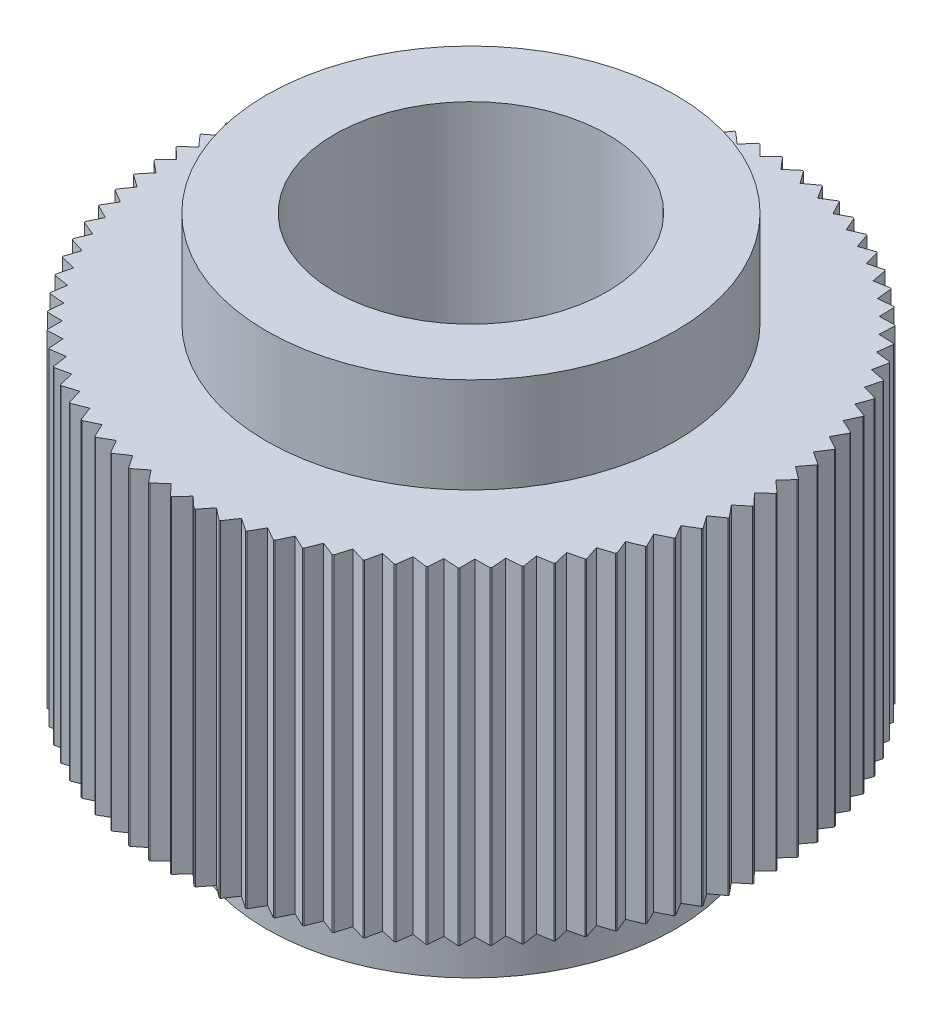
SolidWorks part; units mm, degrees
ref_plane "前视基准面" through (0, 0, 0) normal (0, 0, 1) x (1, 0, 0)
ref_plane "上视基准面" through (0, 0, 0) normal (0, 1, 0) x (1, 0, 0)
ref_plane "右视基准面" through (0, 0, 0) normal (1, 0, 0) x (0, 0, -1)
sketch "草图1" plane through (0, 0, 0) normal (0, 1, 0) x (1, 0, 0)
  circle A0 centre (0, 0) radius 11
  dimension "D1" = 22
extrude "凸台-拉伸1" add sketch "草图1" along normal blind 12
sketch "草图2" plane through (0, 0, 0) normal (0, -1, 0) x (1, 0, 0)
  circle A0 centre (0, 0) radius 7.5
  dimension "D1" = 15
extrude "凸台-拉伸2" add sketch "草图2" along normal blind 3.5
sketch "草图3" plane through (0, 12, 0) normal (0, 1, 0) x (1, 0, 0)
  circle A0 centre (0, 0) radius 7.5
  dimension "D1" = 15
extrude "凸台-拉伸3" add sketch "草图3" along normal blind 3.5
sketch "草图4" plane through (0, 15.5, 0) normal (0, 1, 0) x (1, 0, 0)
  circle A0 centre (0, 0) radius 5
  dimension "D1" = 10
extrude "切除-拉伸1" cut sketch "草图4" against normal through all
sketch "草图5" plane through (0, 12, 0) normal (0, 1, 0) x (1, 0, 0)
  line L0 (0, 0) -> (0, 11) construction
  line L1 (0, 10.6) -> (-0.393, 10.993)
  line L2 (0, 10.6) -> (0.393, 10.993)
  circle A0 centre (0, 0) radius 10.6 construction
  circle A1 centre (0, 0) radius 11
  circle A2 centre (0, 0) radius 11
  circle M2 centre (0, 0) radius 11
  dimension "D3" = 90
  dimension "D1" = 0
  dimension "D2" = 0.4
extrude "切除-拉伸2" cut sketch "草图5" against normal through all contours L1 L2 M2
pattern_circular "阵列(圆周)1" count 83 over 360 about axis through (0, 0, 0) along (0, 1, 0) of "切除-拉伸2"
